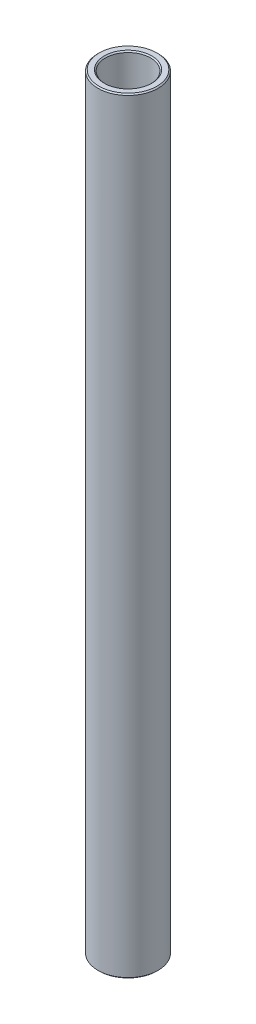
SolidWorks part; units mm, degrees
ref_plane "Front Plane" through (0, 0, 0) normal (0, 0, 1) x (1, 0, 0)
ref_plane "Top Plane" through (0, 0, 0) normal (0, 1, 0) x (1, 0, 0)
ref_plane "Right Plane" through (0, 0, 0) normal (1, 0, 0) x (0, 0, -1)
sketch "Sketch1" plane through (0, 0, 0) normal (0, 0, 1) x (1, 0, 0)
  line L0 (4.7625, 124.2592) -> (4.7625, 285.9965)
  line L1 (4.7625, 285.9965) -> (6.35, 285.9965)
  line L2 (6.35, 285.9965) -> (6.35, 124.2592)
  line L3 (6.35, 124.2592) -> (4.7625, 124.2592)
  line L4 (120.0875, 132.9904) -> (10.0875, 132.9904) construction
  line L6 (0, 114.7342) -> (0, 295.5215) construction
  dimension "D1" = 9.525
  dimension "D2" = 9.525
  dimension "D3" = 12.7
  dimension "D4" = 9.525
revolve "Revolve1" add sketch "Sketch1" angle 360 about L6
chamfer "Chamfer1" distance 0.254 angle 45 4 edges at (6.35, 285.9965, 0) (4.7625, 285.9965, 0) (4.7625, 124.2592, 0) (6.35, 124.2592, 0)
equation "\"D4@Sketch1\"=\"D1@Sketch1\""
